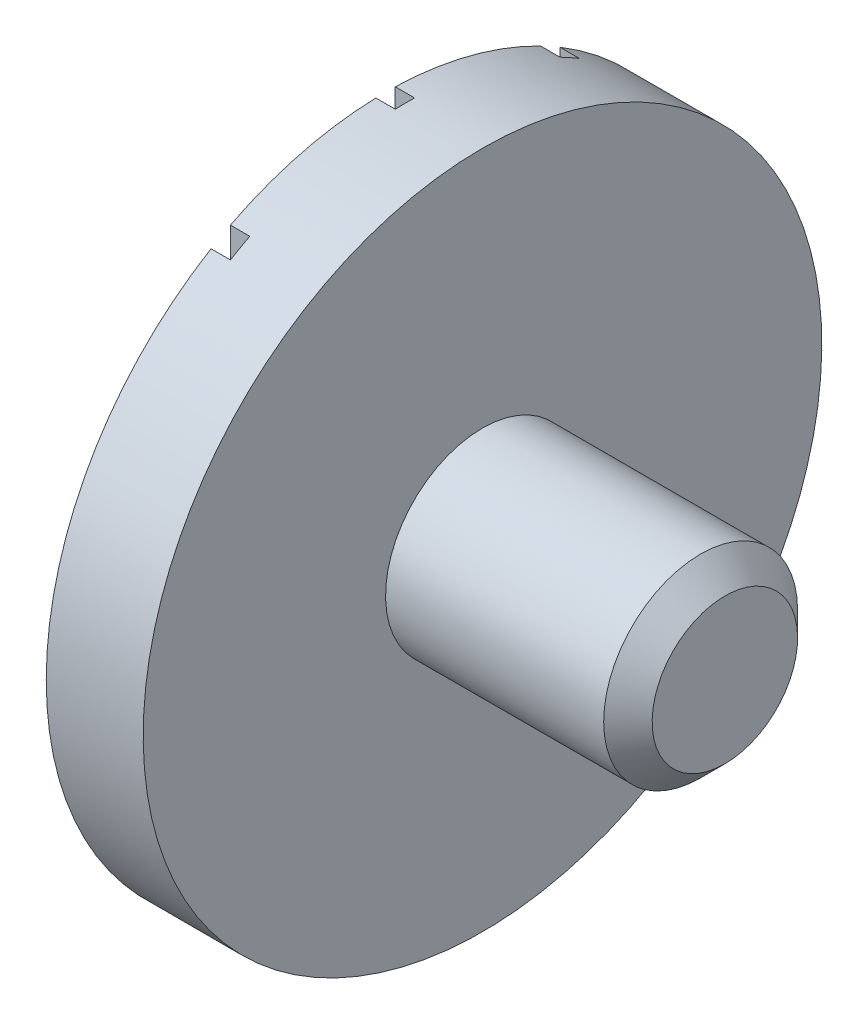
SolidWorks part; units mm, degrees
ref_plane "Alzado" through (0, 0, 0) normal (0, 0, 1) x (1, 0, 0)
ref_plane "Planta" through (0, 0, 0) normal (0, 1, 0) x (1, 0, 0)
ref_plane "Vista lateral" through (0, 0, 0) normal (1, 0, 0) x (0, 0, -1)
sketch "Croquis1" plane through (0, 0, 0) normal (0, 0, 1) x (1, 0, 0)
  line L0 (0, 0) -> (0, -1.75)
  line L1 (0, -1.75) -> (0.5, -1.75)
  line L2 (0.5, -1.75) -> (0.5, -0.5)
  line L3 (0.5, -0.5) -> (1.75, -0.5)
  line L4 (1.75, -0.5) -> (1.75, 0)
  line L5 (1.75, 0) -> (0, 0)
  dimension "D1" = 0.5
  dimension "D2" = 1.75
  dimension "D3" = 0.5
  dimension "D4" = 1.75
revolve "Revolución1" add sketch "Croquis1" angle 360 about L5
cosmetic thread "Rosca cosmética1" parameters "D2"=0.75
chamfer "Chaflán1" distance 0.125 angle 45 1 edges at (1.75, 0.5, 0)
sketch "Croquis7" plane through (0, 0, 0) normal (-1, 0, 0) x (0, 0, 1)
  line L2 (-0.05, -1.7493) -> (-0.05, 1.7493)
  line L4 (0.05, -1.7493) -> (0.05, 1.7493)
  line L6 (0.8, -1.5564) -> (0.8, 1.5564)
  line L8 (0.9, -1.5008) -> (0.9, 1.5008)
  line L10 (-0.9, -1.5008) -> (-0.9, 1.5008)
  line L12 (-0.8, -1.5564) -> (-0.8, 1.5564)
  circle A0 centre (0, 0) radius 1.75 construction
  arc A1 (-0.8, 1.5564) -> (-0.9, 1.5008) centre (0, 0) ccw
  arc A2 (0.05, 1.7493) -> (-0.05, 1.7493) centre (0, 0) ccw
  arc A3 (0.9, 1.5008) -> (0.8, 1.5564) centre (0, 0) ccw
  arc A4 (0.8, -1.5564) -> (0.9, -1.5008) centre (0, 0) ccw
  arc A5 (-0.05, -1.7493) -> (0.05, -1.7493) centre (0, 0) ccw
  arc A6 (-0.9, -1.5008) -> (-0.8, -1.5564) centre (0, 0) ccw
  dimension "D1" = 0.1
  dimension "D2" = 0.1
  dimension "D3" = 0.1
  dimension "D4" = 0.05
  dimension "D5" = 0.75
  dimension "D6" = 0.75
extrude "Cortar-Extruir1" cut sketch "Croquis7" against normal blind 0.1
